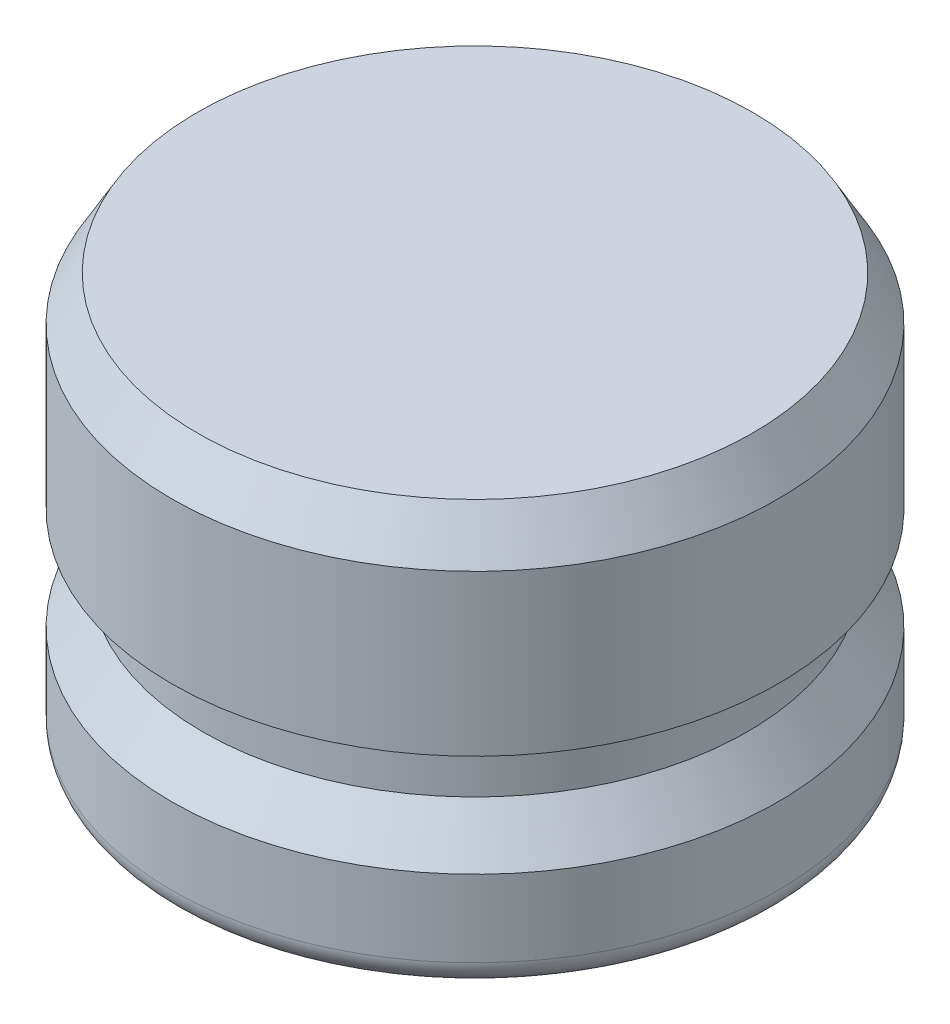
SolidWorks part; units mm, degrees
ref_plane "Front Plane" through (0, 0, 0) normal (0, 0, 1) x (1, 0, 0)
ref_plane "Top Plane" through (0, 0, 0) normal (0, 1, 0) x (1, 0, 0)
ref_plane "Right Plane" through (0, 0, 0) normal (1, 0, 0) x (0, 0, -1)
sketch "Sketch1" plane through (0, 0, 0) normal (0, 0, 1) x (1, 0, 0)
  line L0 (0, 0) -> (0, 12.7) construction
  line L1 (0, 0) -> (-9.4234, 0)
  line L2 (-9.4234, 0) -> (-9.4234, 3.175)
  line L4 (-8.4582, 4.572) -> (-8.4582, 6.35)
  line L5 (-8.4582, 6.35) -> (-9.4234, 6.35)
  line L6 (-9.4234, 6.35) -> (-9.4234, 12.7)
  line L7 (-9.4234, 12.7) -> (0, 12.7)
  line L8 (-9.525, 16.6801) -> (-9.525, -9.6051) construction
  line L9 (0, 0) -> (0, 12.7)
  line L10 (-8.4582, 4.572) -> (-9.4234, 3.175)
  dimension "D1" = 12.7
  dimension "D2" = 9.4234
  dimension "D3" = 1.778
  dimension "D4" = 3.175
  dimension "D5" = 9.525
  dimension "D6" = 8.4582
  dimension "D7" = 6.35
revolve "Revolve1" add sketch "Sketch1" angle 360 about L9
fillet "Fillet1" radius 0.7937 1 edges at (0, 0, -9.4234)
chamfer "Chamfer1" distance 0.7937 angle 60 1 edges at (0, 12.7, -9.4234)
